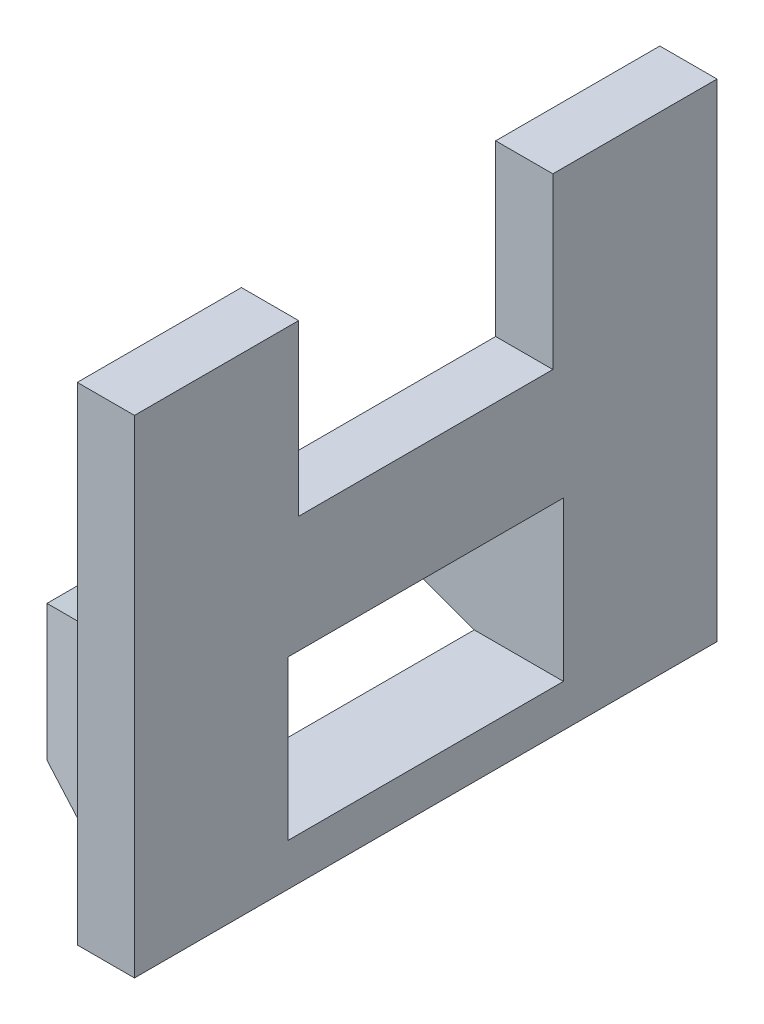
SolidWorks part; units mm, degrees
ref_plane "Front Plane" through (0, 0, 0) normal (0, 0, 1) x (1, 0, 0)
ref_plane "Top Plane" through (0, 0, 0) normal (0, 1, 0) x (1, 0, 0)
ref_plane "Right Plane" through (0, 0, 0) normal (1, 0, 0) x (0, 0, -1)
sketch "Sketch1" plane through (0, 0, 0) normal (1, 0, 0) x (0, 0, -1)
  line L1 (-13.75, 11.5) -> (13.75, 11.5)
  line L2 (-13.75, 11.5) -> (-13.75, -11.5)
  line L3 (-13.75, -11.5) -> (13.75, -11.5)
  line L4 (13.75, 11.5) -> (13.75, -11.5)
  line L5 (-13.75, 11.5) -> (13.75, -11.5) construction
  line L6 (-13.75, -11.5) -> (13.75, 11.5) construction
  line L12 (-13, 10.05) -> (13, 10.05) construction
  line L13 (-13, 10.05) -> (-13, -10.05) construction
  line L14 (-13, -10.05) -> (13, -10.05) construction
  line L15 (13, 10.05) -> (13, -10.05) construction
  line L16 (-13, 10.05) -> (13, -10.05) construction
  line L17 (-13, -10.05) -> (13, 10.05) construction
  point P0 (0, 0)
  point P17 (0, 0)
  dimension "D1" = 27.5
  dimension "D2" = 23
  dimension "D6" = 26
  dimension "D7" = 20.1
extrude "Boss-Extrude1" add sketch "Sketch1" against normal blind 2.7
sketch "Sketch2" plane through (0, 0, 0) normal (1, 0, 0) x (0, 0, -1)
  line L0 (-6, 11.5) -> (-6, 3.5)
  line L1 (-13.75, 11.5) -> (13.75, 11.5) construction
  line L2 (-6, 3.5) -> (6, 3.5)
  line L3 (6, 3.5) -> (6, 11.5)
  line L6 (-6, 11.5) -> (6, 11.5)
  line L7 (13, 10.05) -> (13, -10.05) construction
  line L8 (-13, 10.05) -> (-13, -10.05) construction
  dimension "D1" = 8
  dimension "D2" = 7
  dimension "D3" = 7
extrude "Cut-Extrude1" cut sketch "Sketch2" against normal through all
sketch "Sketch3" plane through (0, 0, 0) normal (1, 0, 0) x (0, 0, -1)
  line L0 (-13.75, -11.5) -> (13.75, -11.5) construction
  line L1 (-4.5, -7.5) -> (4.5, -7.5)
  line L2 (-4.5, -7.5) -> (-4.5, -4)
  line L3 (-4.5, -4) -> (4.5, -4)
  line L4 (4.5, -7.5) -> (4.5, -4)
  line L8 (-6.5, -9.5) -> (-6.5, -2)
  line L9 (-6.5, -2) -> (6.5, -2)
  line L10 (6.5, -9.5) -> (6.5, -2)
  line L11 (-6.5, -9.5) -> (6.5, -9.5)
  point P4 (0, -4)
  dimension "D1" = 3.5
  dimension "D3" = 9
  dimension "D5" = 7.5
  dimension "D4" = 2
ref_plane "Plane1" through (-7.7, 0, 0) normal (-1, 0, 0) x (0, 0, 1)
sketch "Sketch4" plane through (-2.7, 0, 0) normal (-1, 0, 0) x (0, 0, 1)
  line L0 (-13, 10.05) -> (-13, -10.05) construction
  line L5 (-12, 0) -> (12, 0)
  line L6 (-12, 0) -> (-12, -10.05)
  line L7 (-12, -10.05) -> (12, -10.05)
  line L8 (12, 0) -> (12, -10.05)
  line L9 (13, 10.05) -> (13, -10.05) construction
  line L11 (13, -10.05) -> (-13, -10.05) construction
  dimension "D1" = 1
  dimension "D2" = 1
extrude "Boss-Extrude4" add sketch "Sketch4" along normal blind 5 draft 20
extrude "Cut-Extrude3" cut sketch "Sketch3" against normal up to surface (7.7 mm away) contours L9 L10 L11 L8 up to face at (-7.7, -5.025, 0)
